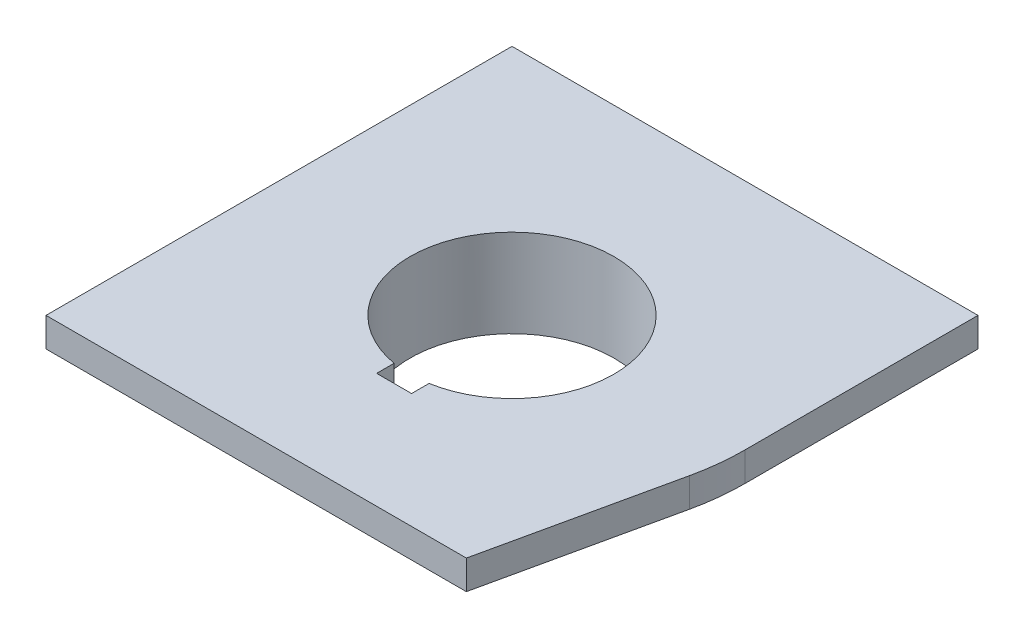
SolidWorks part; units mm, degrees
ref_plane "Front Plane" through (0, 0, 0) normal (0, 0, 1) x (1, 0, 0)
ref_plane "Top Plane" through (0, 0, 0) normal (0, 1, 0) x (1, 0, 0)
ref_plane "Right Plane" through (0, 0, 0) normal (1, 0, 0) x (0, 0, -1)
sketch "Sketch1" plane through (0, 0, 0) normal (0, 1, 0) x (1, 0, 0)
  line L1 (25.4, -25.4) -> (-25.4, -25.4)
  line L2 (25.4, -25.4) -> (25.4, 25.4)
  line L3 (25.4, 25.4) -> (-25.4, 25.4)
  line L4 (-25.4, -25.4) -> (-25.4, 25.4)
  line L5 (25.4, -25.4) -> (-25.4, 25.4) construction
  line L6 (25.4, 25.4) -> (-25.4, -25.4) construction
  circle A0 centre (0, 0) radius 11.1125
  dimension "D1" = 22.225
  dimension "D2" = 50.8
  dimension "D3" = 50.8
extrude "Boss-Extrude1" add sketch "Sketch1" along normal blind 3.175
sketch "Sketch2" plane through (0, 0, 0) normal (0, -1, 0) x (1, 0, 0)
  line L0 (0, 0) -> (-1.8253, 17.3668) construction
  line L1 (0, 0) -> (0, 25.4) construction
  line L2 (-25.4, 25.4) -> (25.4, 25.4) construction
  arc A0 (-14.0769, 2.3684) -> (-13.2769, -5.2434) centre (0, 0) ccw
  circle A1 centre (0, 0) radius 11.1125 construction
  circle A2 centre (0, 0) radius 11.1125
  arc A3 (-4.9874, 13.3752) -> (-3.5312, 15.4723) centre (-5.7693, 15.4723) ccw
  arc A4 (-3.5312, 15.4723) -> (-1.8253, 17.3668) centre (-1.6262, 15.4723) cw
  arc A5 (-1.8253, 17.3668) -> (0.2372, 15.8683) centre (-1.6262, 15.4723) cw
  arc A6 (0.2372, 15.8683) -> (2.0975, 14.1199) centre (2.4264, 16.3337) ccw
  arc A7 (9.0896, 11.0068) -> (11.6338, 10.7942) centre (10.5147, 12.7325) ccw
  arc A8 (13.861, 7.7288) -> (13.2769, 5.2434) centre (15.3586, 6.0655) ccw
  arc A9 (14.1275, 10.2642) -> (13.861, 7.7288) centre (12.5863, 9.1445) cw
  arc A10 (11.6338, 10.7942) -> (14.1275, 10.2642) centre (12.5863, 9.1445) cw
  arc A11 (14.0769, -2.3684) -> (15.165, -4.678) centre (16.284, -2.7398) ccw
  arc A12 (13.6238, -8.1396) -> (11.1794, -8.8764) centre (12.9322, -10.2681) ccw
  arc A13 (15.9528, -7.1026) -> (13.6238, -8.1396) centre (14.2125, -6.3278) cw
  arc A14 (15.165, -4.678) -> (15.9528, -7.1026) centre (14.2125, -6.3278) cw
  arc A15 (4.9874, -13.3752) -> (3.5312, -15.4723) centre (5.7693, -15.4723) ccw
  arc A16 (-0.2372, -15.8683) -> (-2.0975, -14.1199) centre (-2.4264, -16.3337) ccw
  arc A17 (1.8253, -17.3668) -> (-0.2372, -15.8683) centre (1.6262, -15.4723) cw
  arc A18 (3.5312, -15.4723) -> (1.8253, -17.3668) centre (1.6262, -15.4723) cw
  arc A19 (-9.0896, -11.0068) -> (-11.6338, -10.7942) centre (-10.5147, -12.7325) ccw
  arc A20 (-13.861, -7.7288) -> (-13.2769, -5.2434) centre (-15.3586, -6.0655) ccw
  arc A21 (-14.1275, -10.2642) -> (-13.861, -7.7288) centre (-12.5863, -9.1445) cw
  arc A22 (-11.6338, -10.7942) -> (-14.1275, -10.2642) centre (-12.5863, -9.1445) cw
  arc A23 (-14.0769, 2.3684) -> (-15.165, 4.678) centre (-16.284, 2.7398) ccw
  arc A24 (-13.6238, 8.1396) -> (-11.1794, 8.8764) centre (-12.9322, 10.2681) ccw
  arc A25 (-15.9528, 7.1026) -> (-13.6238, 8.1396) centre (-14.2125, 6.3278) cw
  arc A26 (-15.165, 4.678) -> (-15.9528, 7.1026) centre (-14.2125, 6.3278) cw
  arc A27 (-4.9874, 13.3752) -> (-11.1794, 8.8764) centre (0, 0) ccw
  arc A28 (9.0896, 11.0068) -> (2.0975, 14.1199) centre (0, 0) ccw
  arc A29 (14.0769, -2.3684) -> (13.2769, 5.2434) centre (0, 0) ccw
  arc A30 (4.9874, -13.3752) -> (11.1794, -8.8764) centre (0, 0) ccw
  arc A31 (-9.0896, -11.0068) -> (-2.0975, -14.1199) centre (0, 0) ccw
  point P64 (0, 0)
  dimension "D1" = 28.5496
  dimension "D3" = 1.905
  dimension "D2" = 15.5575
  dimension "D5" = 6
  dimension "D6" = 6
extrude "Boss-Extrude2" add sketch "Sketch2" along normal blind 3.2385
sketch "Sketch3" plane through (0, -3.2385, 0) normal (0, -1, 0) x (1, 0, 0)
  arc A0 (-13.6238, 8.1396) -> (-11.1794, 8.8764) centre (-12.9322, 10.2681) ccw construction
  arc A1 (-13.6238, 8.1396) -> (-15.165, 4.678) centre (-14.2125, 6.3278) ccw construction
  arc A3 (-14.0769, 2.3684) -> (-13.2769, -5.2434) centre (0, 0) ccw construction
  arc A4 (-13.861, -7.7288) -> (-13.2769, -5.2434) centre (-15.3586, -6.0655) ccw construction
  arc A5 (-13.861, -7.7288) -> (-11.6338, -10.7942) centre (-12.5863, -9.1445) ccw construction
  arc A7 (-9.0896, -11.0068) -> (-2.0975, -14.1199) centre (0, 0) ccw construction
  arc A8 (-0.2372, -15.8683) -> (-2.0975, -14.1199) centre (-2.4264, -16.3337) ccw construction
  arc A9 (-0.2372, -15.8683) -> (3.5312, -15.4723) centre (1.6262, -15.4723) ccw construction
  arc A11 (4.9874, -13.3752) -> (11.1794, -8.8764) centre (0, 0) ccw construction
  arc A12 (13.6238, -8.1396) -> (11.1794, -8.8764) centre (12.9322, -10.2681) ccw construction
  arc A13 (13.6238, -8.1396) -> (15.165, -4.678) centre (14.2125, -6.3278) ccw construction
  arc A15 (14.0769, -2.3684) -> (13.2769, 5.2434) centre (0, 0) ccw construction
  arc A16 (13.861, 7.7288) -> (13.2769, 5.2434) centre (15.3586, 6.0655) ccw construction
  arc A17 (13.861, 7.7288) -> (11.6338, 10.7942) centre (12.5863, 9.1445) ccw construction
  arc A19 (9.0896, 11.0068) -> (2.0975, 14.1199) centre (0, 0) ccw construction
  arc A20 (0.2372, 15.8683) -> (2.0975, 14.1199) centre (2.4264, 16.3337) ccw construction
  arc A21 (0.2372, 15.8683) -> (-3.5312, 15.4723) centre (-1.6262, 15.4723) ccw construction
  arc A23 (-4.9874, 13.3752) -> (-11.1794, 8.8764) centre (0, 0) ccw construction
  circle A24 centre (0, 0) radius 11.1125 construction
  arc A25 (-13.6238, 8.1396) -> (-11.1794, 8.8764) centre (-12.9322, 10.2681) ccw
  arc A26 (-13.6238, 8.1396) -> (-15.9528, 7.1026) centre (-14.2125, 6.3278) ccw
  arc A28 (-14.2519, -0.8079) -> (-13.2769, -5.2434) centre (0, 0) ccw
  arc A29 (-13.861, -7.7288) -> (-13.2769, -5.2434) centre (-15.3586, -6.0655) ccw
  arc A30 (-13.861, -7.7288) -> (-14.1275, -10.2642) centre (-12.5863, -9.1445) ccw
  arc A32 (-6.4263, -12.7465) -> (-2.0975, -14.1199) centre (0, 0) ccw
  arc A33 (-0.2372, -15.8683) -> (-2.0975, -14.1199) centre (-2.4264, -16.3337) ccw
  arc A34 (-0.2372, -15.8683) -> (1.8253, -17.3668) centre (1.6262, -15.4723) ccw
  arc A35 (-7.8256, 11.9386) -> (-6.87, 14.3061) centre (-9.0525, 13.8104) ccw
  arc A36 (7.8256, -11.9386) -> (11.1794, -8.8764) centre (0, 0) ccw
  arc A37 (13.6238, -8.1396) -> (11.1794, -8.8764) centre (12.9322, -10.2681) ccw
  arc A38 (13.6238, -8.1396) -> (15.9528, -7.1026) centre (14.2125, -6.3278) ccw
  arc A39 (-1.8253, 17.3668) -> (-5.626, 16.5314) centre (0, 0) ccw
  arc A40 (14.2519, 0.8079) -> (13.2769, 5.2434) centre (0, 0) ccw
  arc A41 (13.861, 7.7288) -> (13.2769, 5.2434) centre (15.3586, 6.0655) ccw
  arc A42 (13.861, 7.7288) -> (14.1275, 10.2642) centre (12.5863, 9.1445) ccw
  arc A43 (-5.626, 16.5314) -> (-6.87, 14.3061) centre (-5.0123, 14.728) ccw
  arc A44 (6.4263, 12.7465) -> (2.0975, 14.1199) centre (0, 0) ccw
  arc A45 (0.2372, 15.8683) -> (2.0975, 14.1199) centre (2.4264, 16.3337) ccw
  arc A46 (0.2372, 15.8683) -> (-1.8253, 17.3668) centre (-1.6262, 15.4723) ccw
  arc A47 (14.1275, 10.2642) -> (11.5036, 13.138) centre (0, 0) ccw
  arc A48 (-7.8256, 11.9386) -> (-11.1794, 8.8764) centre (0, 0) ccw
  circle A49 centre (0, 0) radius 11.1125
  arc A51 (11.5036, 13.138) -> (8.9544, 13.1026) centre (10.2486, 11.7048) ccw
  arc A52 (8.9544, 13.1026) -> (6.4263, 12.7465) centre (7.4339, 14.7449) cw
  arc A53 (-15.9528, 7.1026) -> (-17.1296, 3.3934) centre (0, 0) ccw
  arc A54 (-17.1296, 3.3934) -> (-15.8244, 1.2034) centre (-15.2609, 3.0232) ccw
  arc A55 (-15.8244, 1.2034) -> (-14.2519, -0.8079) centre (-16.4864, -0.9345) cw
  arc A56 (-14.1275, -10.2642) -> (-11.5036, -13.138) centre (0, 0) ccw
  arc A57 (-11.5036, -13.138) -> (-8.9544, -13.1026) centre (-10.2486, -11.7048) ccw
  arc A58 (-8.9544, -13.1026) -> (-6.4263, -12.7465) centre (-7.4339, -14.7449) cw
  arc A59 (1.8253, -17.3668) -> (5.626, -16.5314) centre (0, 0) ccw
  arc A60 (5.626, -16.5314) -> (6.87, -14.3061) centre (5.0123, -14.728) ccw
  arc A61 (6.87, -14.3061) -> (7.8256, -11.9386) centre (9.0525, -13.8104) cw
  arc A62 (15.9528, -7.1026) -> (17.1296, -3.3934) centre (0, 0) ccw
  arc A63 (17.1296, -3.3934) -> (15.8244, -1.2034) centre (15.2609, -3.0232) ccw
  arc A64 (15.8244, -1.2034) -> (14.2519, 0.8079) centre (16.4864, 0.9345) cw
  dimension "D1" = 10.16
  dimension "D2" = 10.16
  dimension "D3" = 10.16
  dimension "D4" = 10.16
  dimension "D5" = 10.16
  dimension "D6" = 10.16
extrude "Boss-Extrude3" add sketch "Sketch3" along normal blind 3.175
sketch "Sketch4" plane through (0, 3.175, 0) normal (0, 1, 0) x (1, 0, 0)
  line L1 (-1.905, -10.948) -> (1.905, -10.948)
  line L2 (-1.905, -10.948) -> (-1.905, -12.853)
  line L3 (-1.905, -12.853) -> (1.905, -12.853)
  line L4 (1.905, -10.948) -> (1.905, -12.853)
  circle A0 centre (0, 0) radius 11.1125 construction
  dimension "D1" = 3.81
  dimension "D2" = 1.905
extrude "Cut-Extrude1" cut sketch "Sketch4" against normal blind 1.905
sketch "Sketch5" plane through (0, 0, 0) normal (0, -1, 0) x (1, 0, 0)
  line L0 (0, 0) -> (-3.749, 17.0553) construction
  line L1 (20.4231, 25.4) -> (24.8077, 5.4531)
  line L2 (-25.4, 25.4) -> (25.4, 25.4) construction
  line L3 (25.4, 25.4) -> (25.4, -25.4) construction
  line L4 (25.4, 0) -> (25.4, 25.4)
  line L5 (25.4, 25.4) -> (20.4231, 25.4)
  arc A0 (-1.8253, 17.3668) -> (-5.626, 16.5314) centre (0, 0) ccw construction
  arc A1 (24.8077, 5.4531) -> (25.4, 0) centre (0, 0) cw
extrude "Cut-Extrude2" cut sketch "Sketch5" against normal through all
equation "\"D2@Sketch3\"=\"D1@Sketch3\""
equation "\"D3@Sketch3\"=\"D1@Sketch3\""
equation "\"D4@Sketch3\"=\"D1@Sketch3\""
equation "\"D5@Sketch3\"=\"D1@Sketch3\""
equation "\"D6@Sketch3\"=\"D1@Sketch3\""
